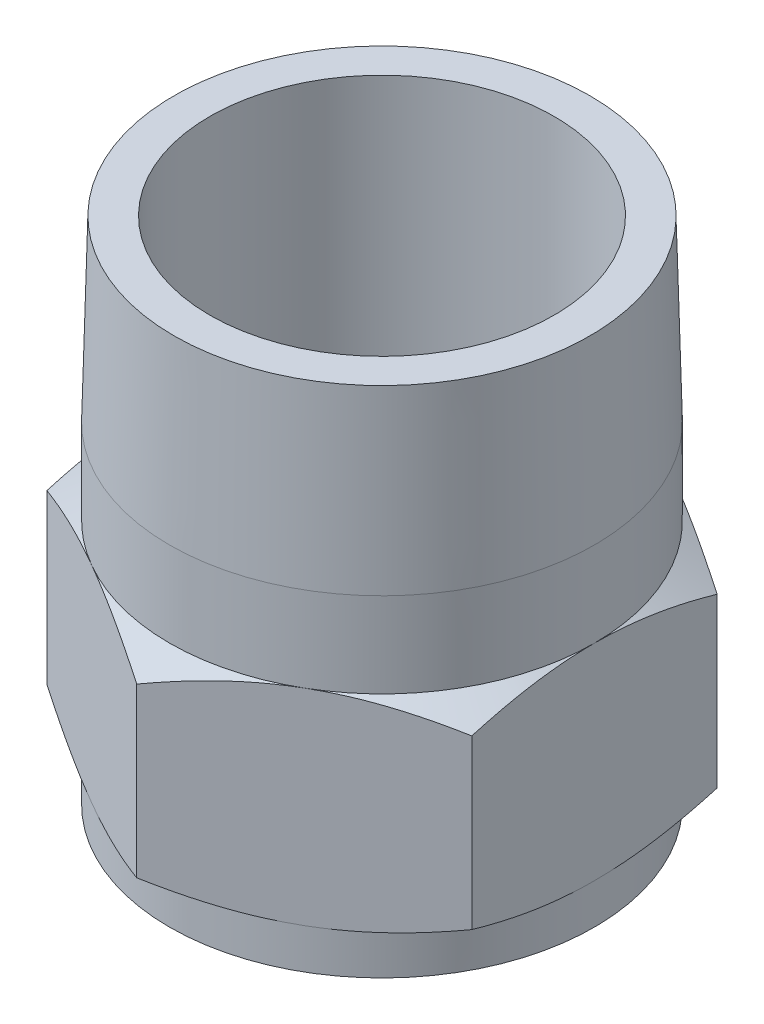
SolidWorks part; units mm, degrees
ref_plane "Front Plane" through (0, 0, 0) normal (0, 0, 1) x (1, 0, 0)
ref_plane "Top Plane" through (0, 0, 0) normal (0, 1, 0) x (1, 0, 0)
ref_plane "Right Plane" through (0, 0, 0) normal (1, 0, 0) x (0, 0, -1)
sketch "Sketch2" plane through (0, 0, 0) normal (0, 1, 0) x (1, 0, 0)
  line L1 (0, 27.4241) -> (-23.75, 13.7121)
  line L2 (-23.75, 13.7121) -> (-23.75, -13.7121)
  line L3 (-23.75, -13.7121) -> (0, -27.4241)
  line L4 (0, -27.4241) -> (23.75, -13.7121)
  line L5 (23.75, -13.7121) -> (23.75, 13.7121)
  line L6 (23.75, 13.7121) -> (0, 27.4241)
  circle A0 centre (0, 0) radius 23.75 construction
  circle A1 centre (0, 0) radius 19.25
  dimension "D1" = 47.5
  dimension "D2" = 4.5
extrude "Boss-Extrude1" add sketch "Sketch2" along normal blind 57
sketch "Sketch3" plane through (0, 0, 0) normal (0, 0, 1) x (1, 0, 0)
  line L0 (0, 57) -> (-23.25, 57)
  line L1 (-23.75, 57) -> (0, 57) construction
  line L2 (-23.25, 57) -> (-23.75, 37)
  line L3 (-23.75, 57) -> (-23.75, 0) construction
  line L7 (-23.75, 4.5) -> (-23.75, 0)
  line L8 (-23.75, 0) -> (-45.6906, 0)
  line L9 (-45.6906, 0) -> (-45.6906, 61.225)
  line L10 (-45.6906, 61.225) -> (0, 61.225)
  line L11 (0, 61.225) -> (0, 57)
  line L13 (-33.75, 21.7265) -> (-33.75, 10.2735)
  line L14 (-33.75, 10.2735) -> (-23.75, 4.5)
  line L15 (-23.75, 37) -> (-23.75, 27.5)
  line L16 (-23.75, 27.5) -> (-33.75, 21.7265)
  dimension "D1" = 23.25
  dimension "D2" = 10
  dimension "D3" = 4.5
  dimension "D4" = 9.5
  dimension "D5" = 60
  dimension "D6" = 20
  dimension "D7" = 60
ref_axis "Axis1" through (0, 64.2862, 0) along (0, -1, 0)
revolve "Cut-Revolve2" cut sketch "Sketch3" angle 360 about axis through (0, 64.2862, 0) along (0, -1, 0)
